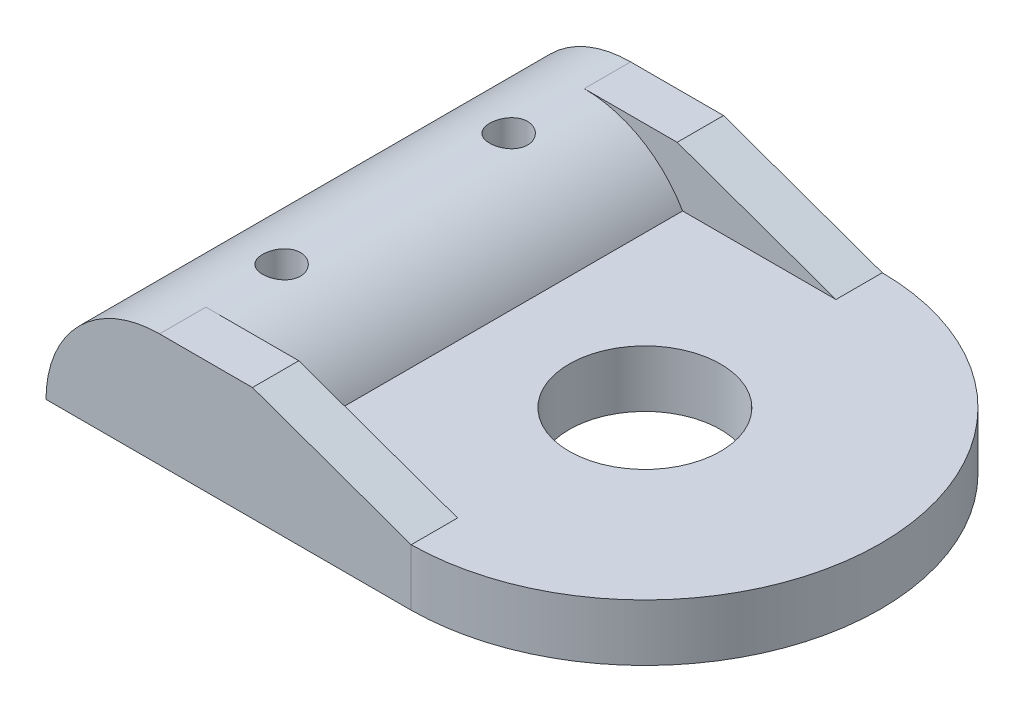
SolidWorks part; units mm, degrees
ref_plane "Alzado" through (0, 0, 0) normal (0, 0, 1) x (1, 0, 0)
ref_plane "Planta" through (0, 0, 0) normal (0, 1, 0) x (1, 0, 0)
ref_plane "Vista lateral" through (0, 0, 0) normal (1, 0, 0) x (0, 0, -1)
sketch "Croquis1" plane through (0, 0, 0) normal (0, 1, 0) x (1, 0, 0)
  line L1 (4.2184, -12.8197) -> (-15.0816, -12.8197)
  line L2 (4.2184, 12.0753) -> (-15.0816, 12.0753)
  line L3 (-15.0816, -12.8197) -> (-15.0816, 12.0753)
  circle A2 centre (4.1192, -0.3722) radius 3.9994
  circle A3 centre (-9.0816, 5.6284) radius 1
  circle A4 centre (-9.0816, -6.3716) radius 1
  arc A8 (4.2184, -12.8197) -> (4.2184, 12.0753) centre (4.1192, -0.3722) ccw
  point P0 (4.2184, 11.9304)
  point P5 (0, 0)
  point P6 (0, 0)
  point P8 (0, 0)
  point P25 (4.1195, -0.3728)
  point P26 (0, 0)
  point P27 (0, 0)
  point P28 (0, 0)
  point P29 (4.1206, -12.8197)
extrude "Saliente-Extruir1" add sketch "Croquis1" along normal blind 3
sketch "Croquis2" plane through (0, 0, 12.8197) normal (0, 0, 1) x (1, 0, 0)
  line L0 (-15.0816, 0) -> (4.2184, 0) construction
  line L1 (-14.2777, 3) -> (-3.8854, 3)
  line L2 (-15.0816, 3) -> (4.2184, 3) construction
  arc A0 (-3.8854, 3) -> (-14.2777, 3) centre (-9.0816, 0) ccw
  dimension "D1" = 12
extrude "Saliente-Extruir2" add sketch "Croquis2" against normal up to surface (24.895 mm away) up to face at (-5.4316, 1.5, -12.0753)
sketch "Croquis3" plane through (0, 3, 0) normal (0, 1, 0) x (1, 0, 0)
  line L0 (-15.0816, 12.0753) -> (-15.0816, -12.8197) construction
  line L1 (4.2184, -12.8197) -> (-9.0816, -12.8197)
  line L2 (4.2184, -12.8197) -> (4.2184, -10.3697)
  line L3 (4.2184, -10.3697) -> (-9.0816, -10.3697)
  line L4 (-9.0816, -12.8197) -> (-9.0816, -10.3697)
  line L5 (4.2184, 12.0753) -> (-9.0816, 12.0753)
  line L6 (4.2184, 12.0753) -> (4.2184, 9.6253)
  line L7 (4.2184, 9.6253) -> (-9.0816, 9.6253)
  line L8 (-9.0816, 12.0753) -> (-9.0816, 9.6253)
  dimension "D1" = 6
  dimension "D2" = 2.45
extrude "Saliente-Extruir3" add sketch "Croquis3" along normal blind 3
sketch "Croquis4" plane through (0, 0, 12.8197) normal (0, 0, 1) x (1, 0, 0)
  line L0 (-4.1716, 6) -> (4.2184, 3)
  line L1 (-9.0816, 6) -> (4.2184, 6) construction
  line L2 (4.2184, 3) -> (4.2184, 6)
  line L3 (4.2184, 6) -> (-4.1716, 6)
  line L4 (-15.0816, 0) -> (4.2184, 0) construction
  line L5 (-15.0816, 0) -> (-16.256, 0)
  line L6 (-9.6833, 5.9698) -> (-9.6833, 7.1492)
  arc A0 (-9.6833, 5.9698) -> (-15.0816, 0) centre (-9.0816, 0) ccw
  arc A1 (-9.6833, 7.1492) -> (-16.256, 0) centre (-9.0816, 0) ccw
  dimension "D2" = 12
  dimension "D1" = 8.39
extrude "Cortar-Extruir1" cut sketch "Croquis4" against normal up to surface (24.895 mm away) up to face at (-5.8956, 3.0995, -12.0753)
sketch "Croquis5" plane through (0, 0, 0) normal (0, -1, 0) x (1, 0, 0)
  circle A0 centre (-9.0816, -5.6284) radius 1 construction
  circle A1 centre (-9.0816, 6.3716) radius 1 construction
  circle A2 centre (-9.0816, -5.6284) radius 1
  circle A3 centre (-9.0816, 6.3716) radius 1
extrude "Cortar-Extruir2" cut sketch "Croquis5" against normal blind 11
